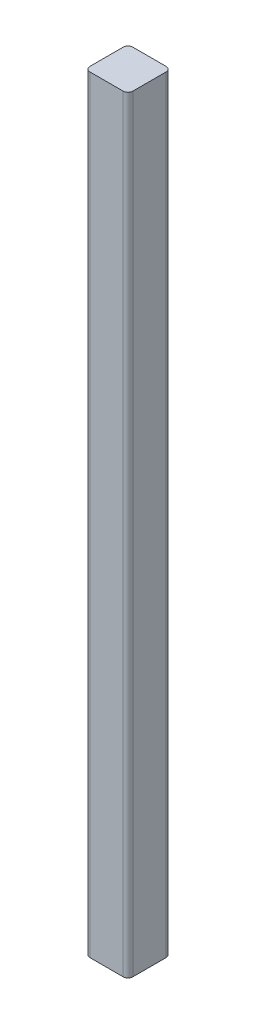
SolidWorks part; units mm, degrees
ref_plane "Front Plane" through (0, 0, 0) normal (0, 0, 1) x (1, 0, 0)
ref_plane "Top Plane" through (0, 0, 0) normal (0, 1, 0) x (1, 0, 0)
ref_plane "Right Plane" through (0, 0, 0) normal (1, 0, 0) x (0, 0, -1)
sketch "Sketch1" plane through (0, 0, 0) normal (0, 1, 0) x (1, 0, 0)
  line L1 (-20, 20) -> (20, 20)
  line L2 (-20, 20) -> (-20, -20)
  line L3 (-20, -20) -> (20, -20)
  line L4 (20, 20) -> (20, -20)
  line L5 (-20, 20) -> (20, -20) construction
  line L6 (-20, -20) -> (20, 20) construction
  point P0 (0, 0)
  dimension "D1" = 40
  dimension "D2" = 40
extrude "Boss-Extrude1" add sketch "Sketch1" along normal blind 715
fillet "Fillet1" radius 4.5 4 edges at (-20, 357.5, -20) (-20, 357.5, 20) (20, 357.5, -20) (20, 357.5, 20)
